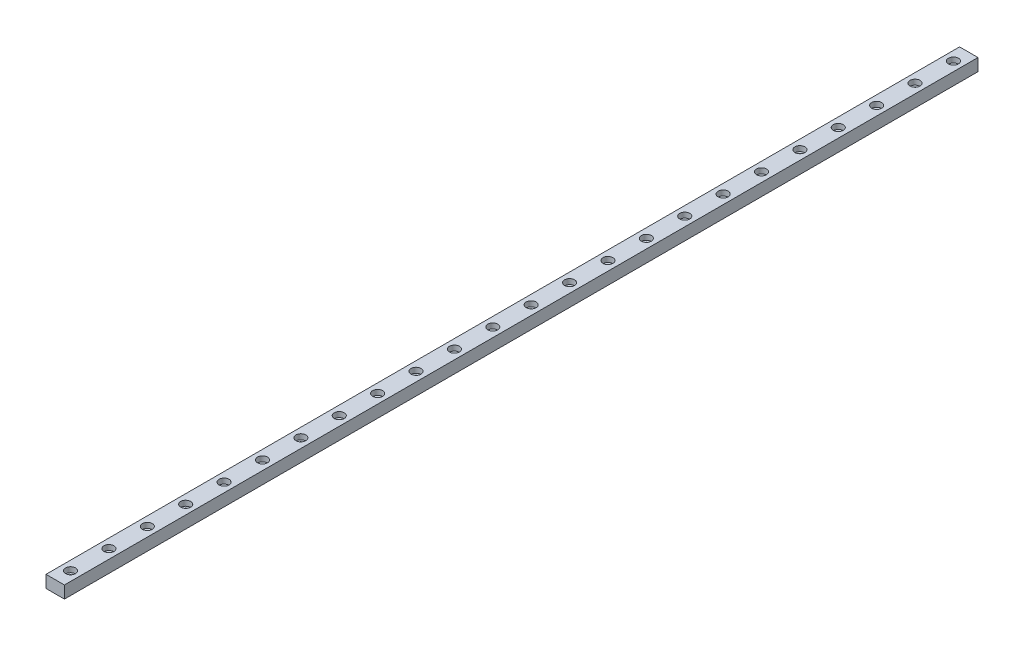
SolidWorks part; units mm, degrees
ref_plane "前视基准面" through (0, 0, 0) normal (0, 0, 1) x (1, 0, 0)
ref_plane "上视基准面" through (0, 0, 0) normal (0, 1, 0) x (1, 0, 0)
ref_plane "右视基准面" through (0, 0, 0) normal (1, 0, 0) x (0, 0, -1)
sketch "草图1" plane through (0, 0, 0) normal (0, 0, 1) x (1, 0, 0)
  line L1 (0, 0) -> (12, 0)
  line L2 (0, 0) -> (0, 8)
  line L3 (0, 8) -> (12, 8)
  line L4 (12, 0) -> (12, 8)
  dimension "D1" = 12
  dimension "D2" = 8
extrude "凸台-拉伸1" add sketch "草图1" along normal blind 595
hole_wizard "M3 六角凹头螺钉的柱形沉头孔1" positions "草图2" profile "草图3" counterbore size "M3" standard "ISO" end condition through all
sketch "草图2" plane through (0, 8, 0) normal (0, 1, 0) x (1, 0, 0)
  line L0 (0, -595) -> (0, 0) construction
  line L1 (12, -595) -> (0, -595) construction
  point P0 (6, -585)
  dimension "D1" = 6
  dimension "D2" = 10
sketch "草图3" plane through (6, 8, 585) normal (1, 0, 0) x (0, 0, 1)
  line L0 (0, 0) -> (0, 8)
  line L1 (0, 8) -> (1.7, 8)
  line L3 (1.7, 8) -> (1.7, 3.4)
  line L4 (1.7, 3.4) -> (3.25, 3.4)
  line L5 (3.25, 3.4) -> (3.25, 0)
  line L7 (3.25, 0) -> (0, 0)
  line L11 (0, -6.35) -> (0, 107.95) construction
  dimension "通孔孔直径" = 3.4
  dimension "通孔孔深度" = 8
  dimension "柱形沉头孔直径" = 6.5
  dimension "柱形沉头孔深度" = 3.4
pattern_linear "阵列(线性)1" count 24 spacing 25 along (0, 0, -1) of "M3 六角凹头螺钉的柱形沉头孔1"
